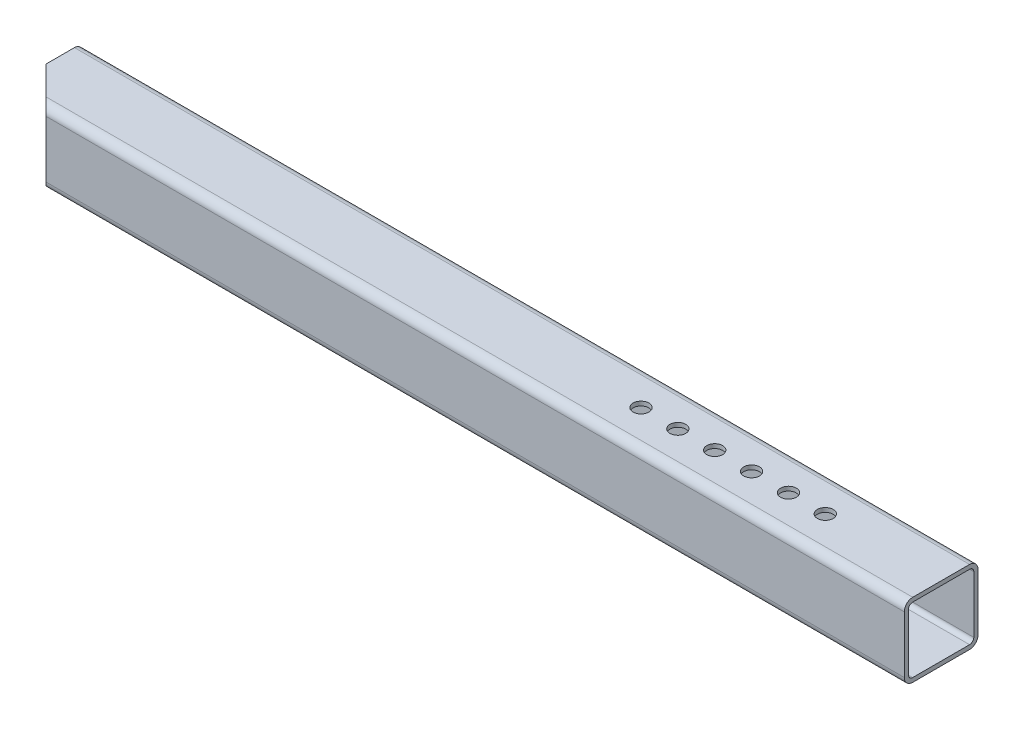
SolidWorks part; units mm, degrees
material "1.0038 (S235JRG2)"
ref_plane "Plan de face" through (0, 0, 0) normal (0, 0, 1) x (1, 0, 0)
ref_plane "Plan de dessus" through (0, 0, 0) normal (0, 1, 0) x (1, 0, 0)
ref_plane "Plan de droite" through (0, 0, 0) normal (1, 0, 0) x (0, 0, -1)
sketch "Esquisse1" plane through (0, 0, 0) normal (0, 0, 1) x (1, 0, 0)
  line L0 (-425, 0) -> (425, 0)
other "Elément mécano-soudé1"
ref_plane "Plan1" through (-425, 0, 0) normal (1, 0, 0) x (0, 1, 0)
sketch "tube carré1" plane through (-425, 0, 0) normal (1, 0, 0) x (0, 1, 0)
  line L0 (-27, 31) -> (27, 31)
  line L1 (-27, 35) -> (27, 35)
  line L2 (-35, 27) -> (-35, -27)
  line L3 (-27, -35) -> (27, -35)
  line L4 (35, 27) -> (35, -27)
  line L5 (31, 27) -> (31, -27)
  line L6 (-27, -31) -> (27, -31)
  line L7 (-31, 27) -> (-31, -27)
  line L8 (-27, 27) -> (-31, 27) construction
  line L9 (-31, 27) -> (-35, 27) construction
  line L10 (-35, 0) -> (35, 0) construction
  line L11 (0, -35) -> (0, 35) construction
  arc A0 (-27, 35) -> (-35, 27) centre (-27, 27) ccw
  arc A1 (-35, -27) -> (-27, -35) centre (-27, -27) ccw
  arc A2 (27, -35) -> (35, -27) centre (27, -27) ccw
  arc A3 (27, 35) -> (35, 27) centre (27, 27) cw
  arc A4 (27, 31) -> (31, 27) centre (27, 27) cw
  arc A5 (27, -31) -> (31, -27) centre (27, -27) ccw
  arc A6 (-31, -27) -> (-27, -31) centre (-27, -27) ccw
  arc A7 (-27, 31) -> (-31, 27) centre (-27, 27) ccw
  point P22 (-35, -35)
  point P24 (35, -35)
  point P25 (35, 35)
  point P26 (-35, 35)
  point P29 (0, 0)
  dimension "C" = 70
  dimension "e" = 4
sketch "Esquisse3" plane through (0, 35, 0) normal (0, 1, 0) x (1, 0, 0)
  line L0 (425, 27) -> (425, -27) construction
  circle A0 centre (315, 0) radius 7.5
  circle A6 centre (280, 0) radius 7.5
  circle A7 centre (245, 0) radius 7.5
  circle A8 centre (210, 0) radius 7.5
  circle A9 centre (175, 0) radius 7.5
  circle A10 centre (140, 0) radius 7.5
  dimension "D1" = 110
  dimension "D2" = 15
  dimension "D3" = 6
extrude "Enlèv. mat.-Extru.2" cut sketch "Esquisse3" against normal blind 90
sketch "Esquisse5" plane through (0, 35, 0) normal (0, 1, 0) x (1, 0, 0)
  line L0 (-425, 0) -> (-390, -35)
  line L3 (-425, 27) -> (-425, -27) construction
  line L5 (425, -35) -> (-425, -35) construction
  line L6 (-390, -35) -> (-425, -35)
  line L7 (-425, -35) -> (-425, 0)
extrude "Enlèv. mat.-Extru.3" cut sketch "Esquisse5" against normal through all
ref_plane "Plan2" through (0, 2, -2) normal (0, -0.7071, 0.7071) x (1, 0, 0)
sketch "Esquisse6" plane through (0, 2, -2) normal (0, -0.7071, 0.7071) x (1, 0, 0)
  line L1 (425, -41.0122) -> (425, -2.8284) construction
  line L2 (-425, -46.1838) -> (425, -46.1838) construction
  circle A0 centre (-155, -56.1838) radius 40.75
  point P2 (425, -21.9203)
  dimension "D1" = 81.5
  dimension "D2" = 580
  dimension "D3" = 10
extrude "Enlèv. mat.-Extru.4" cut sketch "Esquisse6" against normal mid plane 180
ref_plane "Plan3" through (0, 0, 0) normal (0, 0.7071, 0.7071) x (1, 0, 0)
sketch "Esquisse7" [suppressed] plane through (0, 0, 0) normal (0, 0.7071, 0.7071) x (1, 0, 0)
  line L0 (425, 43.8406) -> (425, 5.6569) construction
  line L1 (425, 46.1838) -> (-425, 46.1838) construction
  circle A0 centre (-155, 56.1838) radius 40.75
  dimension "D1" = 81.5
  dimension "D2" = 580
  dimension "D3" = 10
extrude "Enlèv. mat.-Extru.5" [suppressed] cut sketch "Esquisse7" against normal mid plane 150
